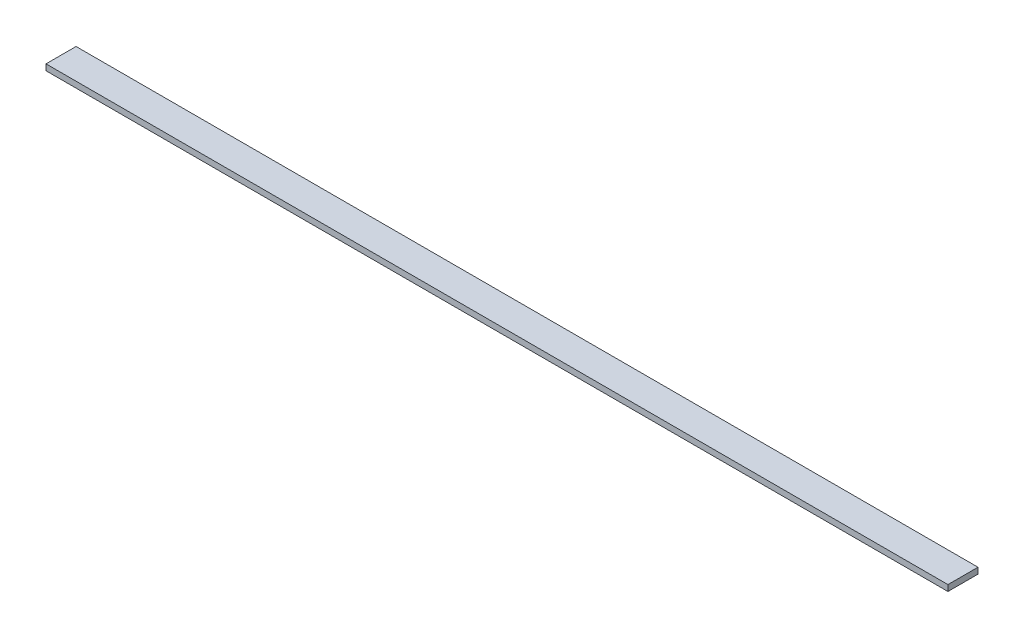
SolidWorks part; units mm, degrees
ref_plane "Спереди" through (0, 0, 0) normal (0, 0, 1) x (1, 0, 0)
ref_plane "Сверху" through (0, 0, 0) normal (0, 1, 0) x (1, 0, 0)
ref_plane "Справа" through (0, 0, 0) normal (1, 0, 0) x (0, 0, -1)
sketch "Эскиз1" plane through (0, 0, 0) normal (0, 1, 0) x (1, 0, 0)
  line L1 (-600, 20) -> (600, 20)
  line L2 (-600, 20) -> (-600, -20)
  line L3 (-600, -20) -> (600, -20)
  line L4 (600, 20) -> (600, -20)
  line L5 (-600, 20) -> (600, -20) construction
  line L6 (-600, -20) -> (600, 20) construction
  point P0 (0, 0)
extrude "Бобышка-Вытянуть1" add sketch "Эскиз1" along normal blind 8
